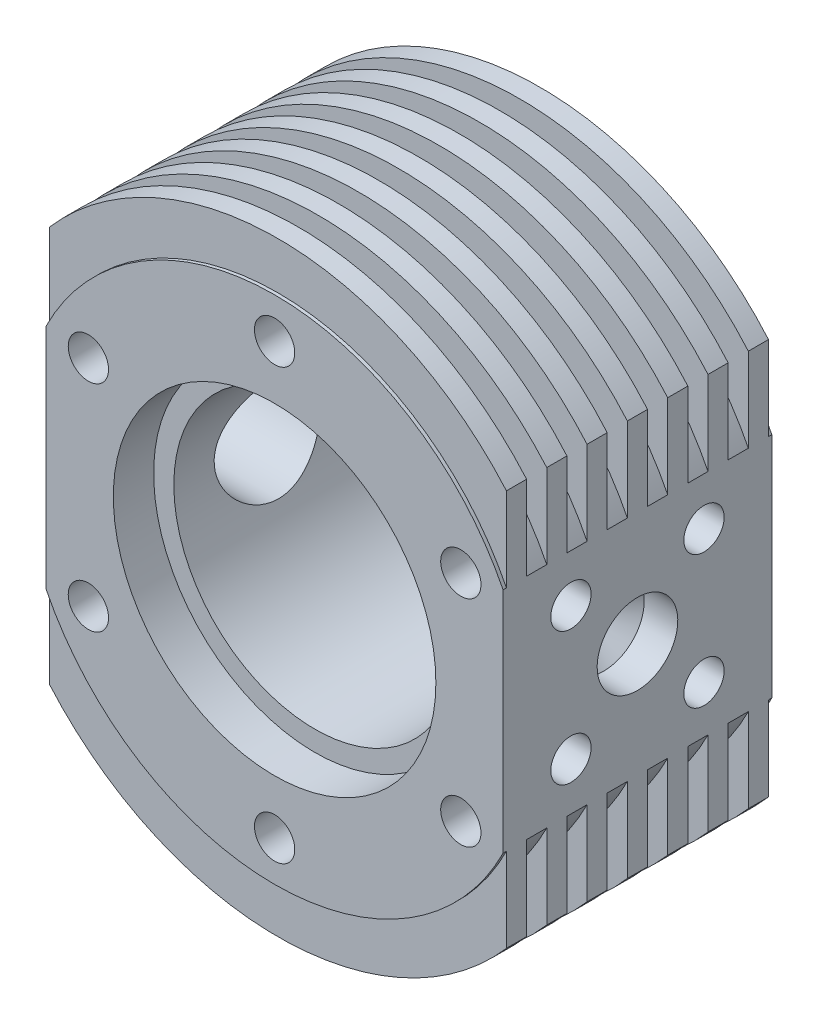
SolidWorks part; units mm, degrees
material "Brass"
ref_plane "Front Plane" through (0, 0, 0) normal (0, 0, 1) x (1, 0, 0)
ref_plane "Top Plane" through (0, 0, 0) normal (0, 1, 0) x (1, 0, 0)
ref_plane "Right Plane" through (0, 0, 0) normal (1, 0, 0) x (0, 0, -1)
sketch "Sketch1" plane through (0, 0, 0) normal (0, 0, 1) x (1, 0, 0)
  line L2 (-17, 14.7394) -> (-17, -14.7394)
  line L4 (17, 14.7394) -> (17, -14.7394)
  line L5 (-17, 27.1233) -> (17, -27.1233) construction
  line L6 (-17, -27.1233) -> (17, 27.1233) construction
  arc A0 (17, 14.7394) -> (-17, 14.7394) centre (0, 0) ccw
  circle A1 centre (0, 0) radius 10.5
  arc A2 (-17, -14.7394) -> (17, -14.7394) centre (0, 0) ccw
  dimension "D1" = 45
  dimension "D2" = 21
  dimension "D3" = 34
extrude "Boss-Extrude1" add sketch "Sketch1" along normal blind 20
sketch "Sketch2" plane through (0, 0, 20) normal (0, 0, 1) x (1, 0, 0)
  circle A0 centre (0, 0) radius 12
  dimension "D1" = 24
extrude "Cut-Extrude1" cut sketch "Sketch2" against normal blind 3
sketch "Sketch3" plane through (0, 0, 0) normal (0, 0, -1) x (-1, 0, 0)
  circle A0 centre (0, 0) radius 19
  dimension "D1" = 38
extrude "Cut-Extrude2" cut sketch "Sketch3" against normal blind 0.25 flip side to cut
sketch "Sketch4" plane through (0, 0, 20) normal (0, 0, 1) x (1, 0, 0)
  circle A0 centre (0, 0) radius 19
  dimension "D1" = 38
extrude "Cut-Extrude3" cut sketch "Sketch4" against normal blind 0.25 flip side to cut
ref_plane "Plane1" through (0, 0, 1.75) normal (0, 0, -1) x (-1, 0, 0)
sketch "Sketch5" plane through (0, 0, 1.75) normal (0, 0, -1) x (-1, 0, 0)
  line L0 (17, 8.4853) -> (17, 14.7394) construction
  line L1 (17, 8.4853) -> (17, 14.7394)
  line L2 (-17, 14.7394) -> (-17, 8.4853) construction
  line L3 (-17, 14.7394) -> (-17, 8.4853)
  arc A0 (17, 8.4853) -> (-17, 8.4853) centre (0, 0) ccw construction
  arc A1 (17, 14.7394) -> (-17, 14.7394) centre (0, 0) ccw construction
  arc A2 (17, 8.4853) -> (-17, 8.4853) centre (0, 0) ccw
  arc A3 (17, 14.7394) -> (-17, 14.7394) centre (0, 0) ccw
extrude "Cut-Extrude4" cut sketch "Sketch5" against normal blind 1.5
pattern_linear "LPattern1" count 6 spacing 3 along (0, 0, 1) of "Cut-Extrude4"
mirror "Mirror1" about plane through (0, 0, 0) normal (0, 1, 0) of "Cut-Extrude4", "LPattern1"
sketch "Sketch6" plane through (-17, 0, 0) normal (-1, 0, 0) x (0, 0, 1)
  line L0 (20, 8.4853) -> (20, -8.4853) construction
  circle A0 centre (10, 0) radius 4
  dimension "D1" = 8
  dimension "D2" = 10
extrude "Cut-Extrude5" cut sketch "Sketch6" against normal up to next
sketch "Sketch7" plane through (-17, 0, 0) normal (-1, 0, 0) x (0, 0, 1)
  circle A1 centre (5.0503, 4.9497) radius 1.5
  circle A2 centre (14.9497, 4.9497) radius 1.5
  circle A3 centre (14.9497, -4.9497) radius 1.5
  circle A4 centre (5.0503, -4.9497) radius 1.5
  point P18 (10, 0)
  dimension "D2" = 3
  dimension "D4" = 4
extrude "Cut-Extrude6" cut sketch "Sketch7" against normal blind 4
ref_plane "Plane2" through (0, 0, 10) normal (0, 0, -1) x (-1, 0, 0)
sketch "Sketch8" plane through (0, 0, 10) normal (0, 0, -1) x (-1, 0, 0)
  line L0 (-17, 0) -> (-17, -3)
  line L1 (-17, -8.4853) -> (-17, 8.4853) construction
  line L2 (-17, -3) -> (-14.5, -3)
  line L3 (-14.5, -3) -> (-11.5, 0)
  line L4 (-11.5, 0) -> (-17, 0)
  dimension "D1" = 3
  dimension "D2" = 2.5
  dimension "D3" = 45
revolve "Cut-Revolve1" cut sketch "Sketch8" angle 360 about L4
mirror "Mirror2" about plane through (0, 0, 0) normal (1, 0, 0) of "Cut-Extrude6"
sketch "Sketch9" plane through (0, 0, 0) normal (0, 0, -1) x (-1, 0, 0)
  circle A0 centre (0, 0) radius 16 construction
  circle A1 centre (0, 16) radius 1.5
  circle A2 centre (13.8564, 8) radius 1.5
  circle A3 centre (13.8564, -8) radius 1.5
  circle A4 centre (0, -16) radius 1.5
  circle A5 centre (-13.8564, -8) radius 1.5
  circle A6 centre (-13.8564, 8) radius 1.5
  point P18 (0, 0)
  dimension "D1" = 32
  dimension "D2" = 3
  dimension "D3" = 6
extrude "Cut-Extrude7" cut sketch "Sketch9" against normal blind 6
mirror "Mirror3" about plane through (0, 0, 10) normal (0, 0, -1) of "Cut-Extrude7"
sketch "Sketch12" plane through (-17, 0, 0) normal (-1, 0, 0) x (0, 0, 1)
